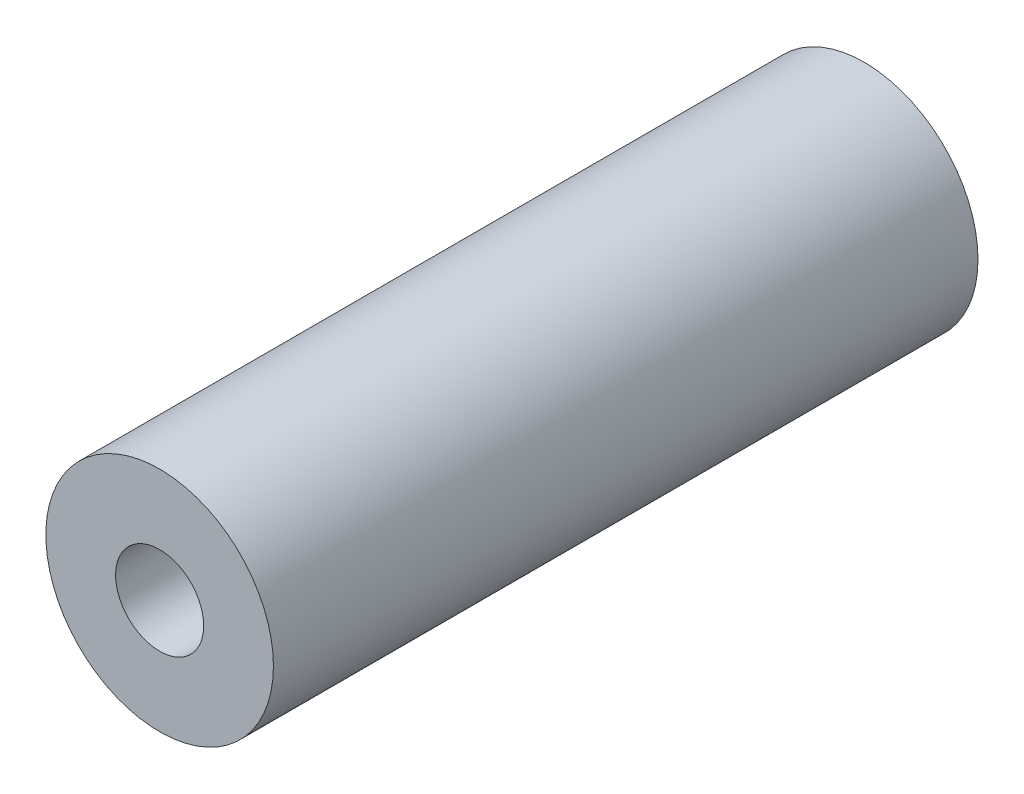
SolidWorks part; units mm, degrees
material "Plain Carbon Steel"
ref_plane "Front Plane" through (0, 0, 0) normal (0, 0, 1) x (1, 0, 0)
ref_plane "Top Plane" through (0, 0, 0) normal (0, 1, 0) x (1, 0, 0)
ref_plane "Right Plane" through (0, 0, 0) normal (1, 0, 0) x (0, 0, -1)
sketch "Sketch1" plane through (0, 0, 0) normal (0, 0, 1) x (1, 0, 0)
  circle A2 centre (-492.1271, 1432.7873) radius 16.4084
  circle A3 centre (-492.1271, 1432.7873) radius 16.4084
  dimension "D1" = 0.1016
extrude "Boss-Extrude1" add sketch "Sketch1" along normal up to surface (101.6 mm away)
ref_plane "Mid Section" through (-492.1271, 0, 0) normal (1, 0, 0) x (0, 0, -1)
sketch "Sketch3" plane through (-492.1271, 0, 0) normal (1, 0, 0) x (0, 0, -1)
  line L0 (-101.6, 1432.7873) -> (0, 1432.7873) construction
  line L1 (-91.44, 1445.3857) -> (-10.16, 1445.3857)
  line L2 (-91.44, 1445.3857) -> (-91.44, 1439.1373)
  line L5 (-101.6, 1449.1957) -> (-101.6, 1416.3789) construction
  line L6 (0, 1416.3789) -> (0, 1449.1957) construction
  line L7 (-50.8, 1449.1957) -> (-50.8, 1416.3789) construction
  line L8 (0, 1449.1957) -> (-101.6, 1449.1957) construction
  line L9 (-101.6, 1416.3789) -> (0, 1416.3789) construction
  line L15 (-101.6, 1439.1373) -> (-91.44, 1439.1373)
  line L16 (-101.6, 1439.1373) -> (-177.8, 1439.1373) construction
  line L17 (-101.6, 1439.1373) -> (-101.6, 1432.7873)
  line L18 (0, 1439.1373) -> (0, 1432.7873)
  line L19 (0, 1439.1373) -> (-10.16, 1439.1373)
  line L20 (-10.16, 1445.3857) -> (-10.16, 1439.1373)
  line L21 (-101.6, 1432.7873) -> (0, 1432.7873)
  point P21 (-50.8, 1445.3857)
  dimension "D1" = 10.16
  dimension "D2" = 3.81
revolve "Cut-Revolve1" cut sketch "Sketch3" angle 360 about L0
